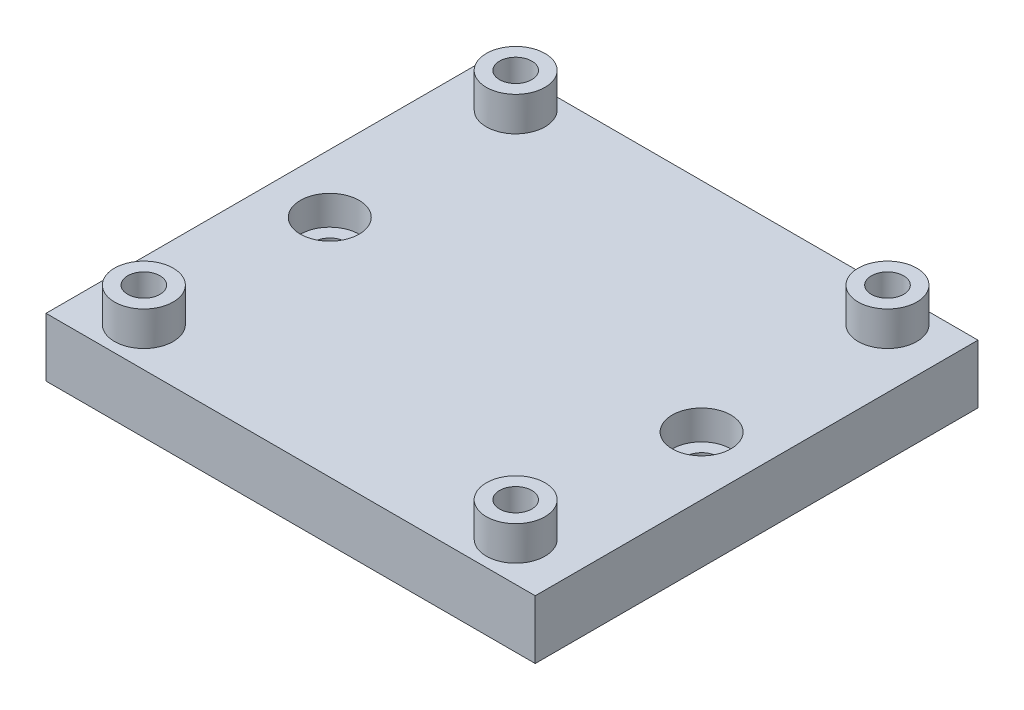
SolidWorks part; units mm, degrees
ref_plane "Front Plane" through (0, 0, 0) normal (0, 0, 1) x (1, 0, 0)
ref_plane "Top Plane" through (0, 0, 0) normal (0, 1, 0) x (1, 0, 0)
ref_plane "Right Plane" through (0, 0, 0) normal (1, 0, 0) x (0, 0, -1)
sketch "Sketch2" plane through (0, 0, 0) normal (0, 1, 0) x (1, 0, 0)
  line L0 (6, 10) -> (44, 10) construction
  line L1 (0, 0) -> (50, 0)
  line L2 (0, 0) -> (0, 55)
  line L3 (0, 55) -> (50, 55)
  line L4 (50, 0) -> (50, 55)
  line L5 (25, 10) -> (25, 48) construction
  line L6 (6, 48) -> (44, 48) construction
  line L7 (6, 29) -> (44, 29) construction
  circle A0 centre (6, 10) radius 1.65
  circle A1 centre (44, 10) radius 1.65
  circle A2 centre (44, 48) radius 1.65
  circle A3 centre (6, 48) radius 1.65
  circle A4 centre (6, 29) radius 1.65
  circle A5 centre (44, 29) radius 1.65
  point P12 (25, 48)
  point P14 (25, 0)
  point P19 (25, 29)
  dimension "D3" = 38
  dimension "D4" = 3.3
  dimension "D5" = 38
  dimension "D1" = 50
  dimension "D2" = 55
  dimension "D6" = 10
extrude "Boss-Extrude2" add sketch "Sketch2" along normal blind 6
sketch "Sketch3" plane through (0, 0, 0) normal (0, 1, 0) x (1, 0, 0)
  line L1 (9.2332, 48) -> (7.6166, 50.8)
  line L2 (7.6166, 50.8) -> (4.3834, 50.8)
  line L3 (4.3834, 50.8) -> (2.7668, 48)
  line L4 (2.7668, 48) -> (4.3834, 45.2)
  line L5 (4.3834, 45.2) -> (7.6166, 45.2)
  line L6 (7.6166, 45.2) -> (9.2332, 48)
  line L7 (47.2332, 48) -> (45.6166, 50.8)
  line L8 (45.6166, 50.8) -> (42.3834, 50.8)
  line L9 (42.3834, 50.8) -> (40.7668, 48)
  line L10 (40.7668, 48) -> (42.3834, 45.2)
  line L11 (42.3834, 45.2) -> (45.6166, 45.2)
  line L12 (45.6166, 45.2) -> (47.2332, 48)
  line L13 (47.2332, 10) -> (45.6166, 12.8)
  line L14 (45.6166, 12.8) -> (42.3834, 12.8)
  line L15 (42.3834, 12.8) -> (40.7668, 10)
  line L16 (40.7668, 10) -> (42.3834, 7.2)
  line L17 (42.3834, 7.2) -> (45.6166, 7.2)
  line L18 (45.6166, 7.2) -> (47.2332, 10)
  line L19 (9.2332, 10) -> (7.6166, 12.8)
  line L20 (7.6166, 12.8) -> (4.3834, 12.8)
  line L21 (4.3834, 12.8) -> (2.7668, 10)
  line L22 (2.7668, 10) -> (4.3834, 7.2)
  line L23 (4.3834, 7.2) -> (7.6166, 7.2)
  line L24 (7.6166, 7.2) -> (9.2332, 10)
  circle A0 centre (6, 48) radius 2.8 construction
  circle A1 centre (44, 48) radius 2.8 construction
  circle A2 centre (44, 10) radius 2.8 construction
  circle A3 centre (6, 10) radius 2.8 construction
  circle A4 centre (6, 10) radius 1.65 construction
  dimension "D1" = 5.6
extrude "Cut-Extrude1" cut sketch "Sketch3" along normal blind 2.4 from offset 1.8
sketch "Sketch4" plane through (0, 6, 0) normal (0, 1, 0) x (1, 0, 0)
  circle A0 centre (6, 10) radius 3
  circle A1 centre (44, 10) radius 3
  circle A2 centre (6, 48) radius 3
  circle A3 centre (44, 48) radius 3
  circle A4 centre (6, 48) radius 1.65
  circle A5 centre (44, 48) radius 1.65
  circle A6 centre (44, 10) radius 1.65
  circle A7 centre (6, 10) radius 1.65
  dimension "D1" = 6
extrude "Boss-Extrude3" add sketch "Sketch4" along normal blind 3.5
sketch "Sketch5" plane through (0, 6, 0) normal (0, 1, 0) x (1, 0, 0)
  circle A0 centre (6, 29) radius 3
  circle A1 centre (44, 29) radius 3
  dimension "D1" = 6
extrude "Cut-Extrude2" cut sketch "Sketch5" against normal blind 3
sketch "Sketch6" plane through (0, 6, 0) normal (0, 1, 0) x (1, 0, 0)
  line L0 (50, 0) -> (50, 55) construction
  line L1 (0, 55) -> (50, 55)
  line L2 (0, 55) -> (0, 51.25)
  line L3 (0, 51.25) -> (50, 51.25)
  line L4 (50, 55) -> (50, 51.25)
  line L6 (0, 0) -> (50, 0)
  line L7 (0, 0) -> (0, 6)
  line L8 (0, 6) -> (50, 6)
  line L9 (50, 0) -> (50, 6)
  dimension "D1" = 3.75
  dimension "D2" = 6
extrude "Cut-Extrude3" cut sketch "Sketch6" against normal blind 10
